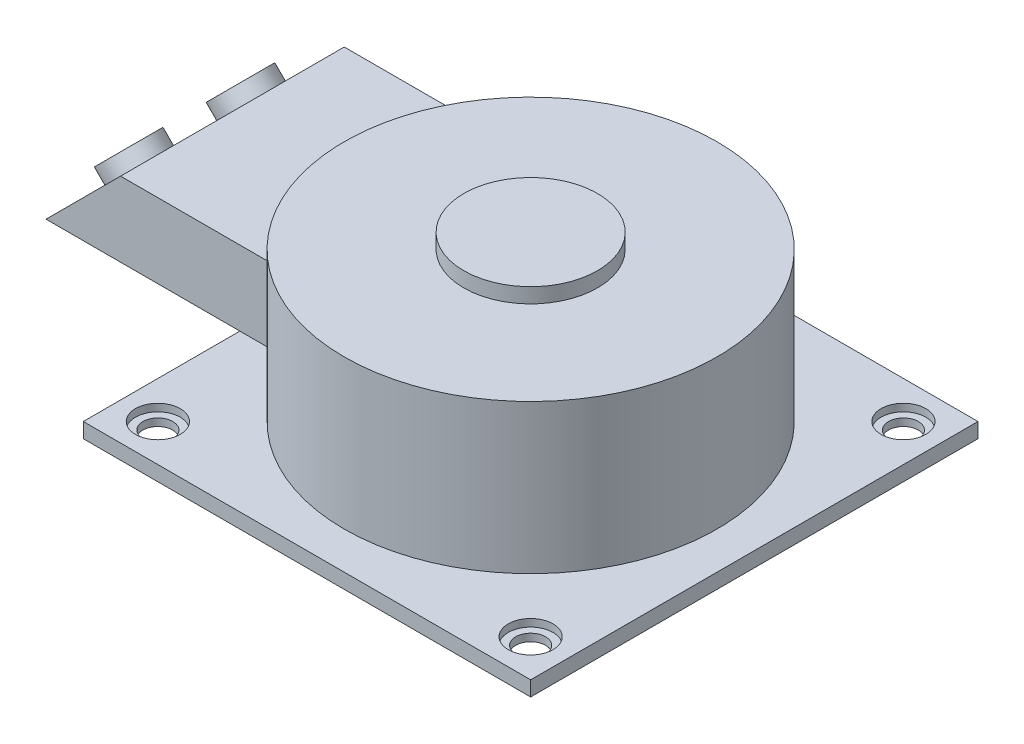
SolidWorks part; units mm, degrees
ref_plane "前视基准面" through (0, 0, 0) normal (0, 0, 1) x (1, 0, 0)
ref_plane "上视基准面" through (0, 0, 0) normal (0, 1, 0) x (1, 0, 0)
ref_plane "右视基准面" through (0, 0, 0) normal (1, 0, 0) x (0, 0, -1)
sketch "草图1" plane through (0, 0, 0) normal (0, 1, 0) x (1, 0, 0)
  line L1 (-150, -150) -> (150, -150)
  line L2 (-150, -150) -> (-150, 150)
  line L3 (-150, 150) -> (150, 150)
  line L4 (150, -150) -> (150, 150)
  line L5 (-150, -150) -> (150, 150) construction
  line L6 (-150, 150) -> (150, -150) construction
  point P0 (0, 0)
  dimension "D1" = 300
  dimension "D2" = 300
extrude "凸台-拉伸1" add sketch "草图1" along normal blind 10
sketch "草图2" plane through (0, 10, 0) normal (0, 1, 0) x (1, 0, 0)
  circle A0 centre (0, 0) radius 125
  dimension "D1" = 250
extrude "凸台-拉伸2" add sketch "草图2" along normal blind 100
sketch "草图3" plane through (0, 0, 0) normal (1, 0, 0) x (0, 0, -1)
  line L3 (-75, 90) -> (75, 90)
  line L4 (-75, 40) -> (75, 40)
  line L6 (0, 0) -> (0, 196.7229) construction
  line L10 (-75, 40) -> (-75, 90)
  line L11 (75, 40) -> (75, 90)
  dimension "D1" = 150
  dimension "D2" = 50
extrude "凸台-拉伸3" add sketch "草图3" against normal blind 200
draft "拔模3" type of draft neutral plane draft angle 45 faces to draft 1 face at (-200, 65, 0) neutral plane through (-200, 90, 75) neutral plane normal (0, 1, 0) parameters "D1"=45
sketch "草图5" plane through (-145, 145, 0) normal (-0.7071, 0.7071, 0) x (0, 0, 1)
  line L0 (0, -148.4924) -> (0, -77.7817) construction
  line L1 (75, -148.4924) -> (-75, -148.4924) construction
  line L2 (-75, -77.7817) -> (75, -77.7817) construction
  line L3 (0, -77.7817) -> (-75, -148.4924) construction
  line L4 (-75, -77.7817) -> (0, -148.4924) construction
  circle A0 centre (-37.5, -113.1371) radius 18.8
  circle A1 centre (37.5, -113.1371) radius 18.8
  dimension "D1" = 37.6
extrude "凸台-拉伸5" add sketch "草图5" along normal blind 10
sketch "草图6" plane through (0, 110, 0) normal (0, 1, 0) x (1, 0, 0)
  circle A0 centre (0, 0) radius 44.85
  dimension "D1" = 89.7
extrude "凸台-拉伸6" add sketch "草图6" along normal blind 10
sketch "草图7" plane through (0, 10, 0) normal (0, 1, 0) x (1, 0, 0)
  line L0 (150, 150) -> (-150, 150) construction
  line L1 (-150, 150) -> (-150, -150) construction
  circle A0 centre (-125, 125) radius 15
  point P4 (0, 0)
  point P6 (-119.3444, 110.3617)
  dimension "D1" = 30
  dimension "D2" = 25
  dimension "D3" = 25
extrude "切除-拉伸1" cut sketch "草图7" against normal blind 5
sketch "草图8" plane through (0, 5, 0) normal (0, 1, 0) x (1, 0, 0)
  circle A0 centre (-125, 125) radius 10
  circle A1 centre (-125, 125) radius 15 construction
  dimension "D1" = 20
extrude "切除-拉伸2" cut sketch "草图8" against normal blind 25
mirror "镜向1" about plane through (0, 0, 0) normal (0, 0, 1) of "切除-拉伸2", "切除-拉伸1"
mirror "镜向2" about plane through (0, 0, 0) normal (1, 0, 0) of "镜向1", "切除-拉伸1", "切除-拉伸2"
